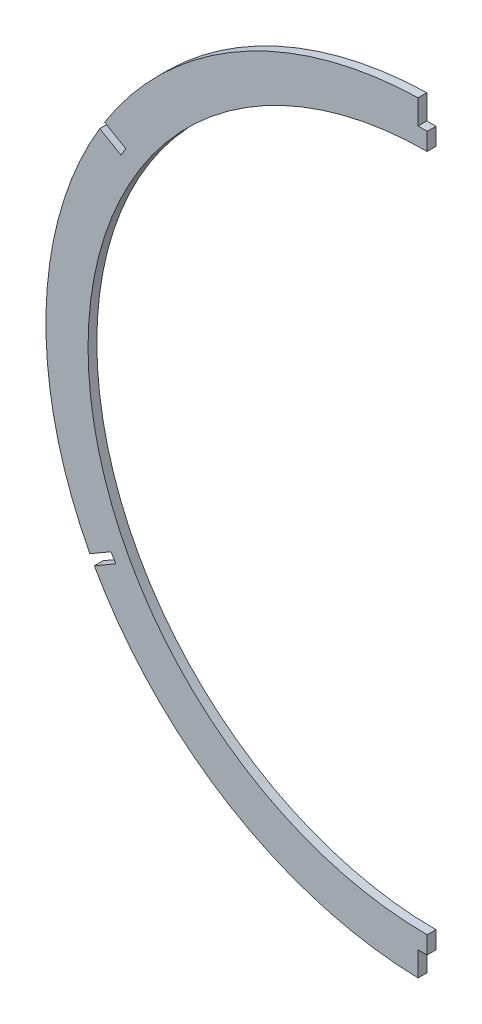
SolidWorks part; units mm, degrees
material "Plywood"
ref_plane "Front Plane" through (0, 0, 0) normal (0, 0, 1) x (1, 0, 0)
ref_plane "Top Plane" through (0, 0, 0) normal (0, 1, 0) x (1, 0, 0)
ref_plane "Right Plane" through (0, 0, 0) normal (1, 0, 0) x (0, 0, -1)
sketch "Sketch1" plane through (0, 0, 0) normal (0, 0, 1) x (1, 0, 0)
  line L0 (0, 0) -> (0, 499.9473) construction
  line L1 (0, -114.7984) -> (0, -129.4545) construction
  line L2 (0, -374.4718) -> (0, 404.2655) construction
  line L3 (-1.651, 142.9921) -> (-1.651, 150.6121) construction
  line L4 (1.651, 142.9921) -> (1.651, 150.6121) construction
  line L5 (-1.651, 142.9921) -> (1.651, 142.9921) construction
  line L6 (136.2041, -53.806) -> (0.0002, 24.7625) construction
  line L7 (-136.2076, -53.7991) -> (0.0002, 24.7625) construction
  line L8 (136.2041, -53.806) -> (0.0002, 24.7625) construction
  line L9 (-136.2076, -53.7991) -> (0.0002, 24.7625) construction
  line L10 (-125.0584, -45.4626) -> (-118.4576, -41.6554) construction
  line L11 (-123.6259, -48.4483) -> (-116.8078, -44.5157) construction
  line L12 (-118.4576, -41.6554) -> (-116.8078, -44.5157) construction
  line L13 (-124.1455, -48.7479) -> (-123.6847, -48.4822) construction
  line L14 (-123.6847, -48.4822) -> (-123.6259, -48.4483) construction
  line L15 (-125.7952, -45.8876) -> (-125.1113, -45.4931) construction
  line L16 (-125.1113, -45.4931) -> (-125.0584, -45.4626) construction
  line L17 (125.4797, -45.7137) -> (125.1075, -45.499) construction
  line L18 (123.8298, -48.5739) -> (123.6807, -48.488) construction
  line L19 (117.0223, -44.647) -> (118.6722, -41.7868) construction
  line L20 (123.6807, -48.488) -> (123.6228, -48.4545) construction
  line L21 (123.6228, -48.4545) -> (117.0223, -44.647) construction
  line L22 (125.1075, -45.499) -> (125.0554, -45.4689) construction
  line L23 (125.0554, -45.4689) -> (118.6722, -41.7868) construction
  line L24 (-107.079, -46.8884) -> (-120.3798, -54.5735)
  line L25 (-108.6638, -44.1348) -> (-121.9647, -51.8199)
  line L28 (-115.4206, -47.9666) -> (-121.9445, -51.7361) construction
  line L29 (-120.2754, -54.5131) -> (-108.646, -44.1245) construction
  line L30 (-114.4607, -49.3188) -> (-122.1124, -53.7399) construction
  line L31 (-113.7686, -50.8257) -> (-120.3665, -54.6379) construction
  line L32 (-115.4206, -47.9666) -> (-113.7686, -50.8257) construction
  line L33 (106.3137, -46.4532) -> (129.9098, -60.0883)
  line L34 (107.9004, -43.7007) -> (131.505, -57.3407)
  line L35 (129.9098, -60.0883) -> (131.505, -57.3407)
  line L36 (129.9098, -60.0883) -> (131.505, -57.3407) construction
  line L37 (107.9004, -43.7007) -> (131.505, -57.3407) construction
  line L38 (106.3137, -46.4532) -> (129.9098, -60.0883) construction
  line L39 (129.9098, -60.0883) -> (107.9004, -43.7007) construction
  line L40 (118.9051, -51.8945) -> (101.8722, -42.0519) construction
  line L41 (120.3631, -54.6438) -> (113.7655, -50.8313)
  line L42 (122.0152, -51.7848) -> (122.0057, -51.7794) construction
  line L43 (113.7655, -50.8313) -> (115.4176, -47.9723)
  line L44 (122.0057, -51.7794) -> (121.9413, -51.7421) construction
  line L45 (121.9413, -51.7421) -> (115.4176, -47.9723)
  line L46 (-108.6638, -44.1348) -> (-121.9647, -51.8199)
  line L47 (-107.079, -46.8884) -> (-120.3798, -54.5735)
  arc A0 (-1.651, 150.6121) -> (-125.0584, -45.4626) centre (0, 12.7) ccw
  circle A1 centre (0, 12.7) radius 120.904
  arc A2 (0, 150.622) -> (-1.651, 150.6121) centre (0, 12.7) ccw
  circle A3 centre (0, 12.7) radius 137.922 construction
  arc A4 (1.651, 150.6121) -> (0, 150.622) centre (0, 12.7) ccw
  arc A5 (-124.3508, -46.9604) -> (-123.6259, -48.4483) centre (0, 12.7) ccw
  arc A6 (-123.6259, -48.4483) -> (-121.9445, -51.7361) centre (0, 12.7) ccw
  arc A7 (-125.0584, -45.4626) -> (-124.3508, -46.9604) centre (0, 12.7) ccw
  arc A8 (124.3477, -46.9667) -> (125.0554, -45.4689) centre (0, 12.7) ccw
  arc A9 (125.0554, -45.4689) -> (1.651, 150.6121) centre (0, 12.7) ccw
  arc A10 (123.6228, -48.4545) -> (124.3477, -46.9667) centre (0, 12.7) ccw
  arc A11 (-121.9153, -51.7914) -> (-121.1641, -53.1919) centre (0, 12.7) ccw
  arc A12 (-120.3665, -54.6379) -> (120.3631, -54.6438) centre (0, 12.7) ccw
  arc A13 (-121.9445, -51.7361) -> (-121.9153, -51.7914) centre (0, 12.7) ccw
  arc A14 (-121.1641, -53.1919) -> (-120.3827, -54.6089) centre (0, 12.7) ccw
  arc A15 (-120.3827, -54.6089) -> (-120.397, -54.5834) centre (0, 12.7) ccw construction
  arc A16 (-120.397, -54.5834) -> (-120.3665, -54.6379) centre (0, 12.7) ccw construction
  arc A17 (120.3936, -54.5893) -> (121.0149, -53.4654) centre (0, 12.7) ccw construction
  arc A18 (121.9413, -51.7421) -> (123.6228, -48.4545) centre (0, 12.7) ccw
  arc A19 (120.3631, -54.6438) -> (120.3936, -54.5893) centre (0, 12.7) ccw construction
  arc A20 (121.0149, -53.4654) -> (121.9121, -51.7974) centre (0, 12.7) ccw construction
  arc A21 (121.9121, -51.7974) -> (121.9413, -51.7421) centre (0, 12.7) ccw construction
  spline S0 degree 3 poles (106.3137, -46.4532) (106.8426, -45.5357) (107.3715, -44.6182) (107.9004, -43.7007) knots 0 0 0 0 1 1 1 1 weights 1 1 1 1
  spline S1 degree 3 poles (-66.0123, 133.6164) (-70.0128, 131.4329) (-73.8716, 129.0699) (-81.3156, 123.9975) (-84.9009, 121.288) (-91.7995, 115.5249) (-95.113, 112.4712) (-99.0811, 108.4341) (-99.866, 107.6157) (-101.4182, 105.9565) (-102.1865, 105.1147) (-104.4569, 102.5643) (-105.9223, 100.8334) (-110.1768, 95.5512) (-115.4725, 88.2691) (-120.0285, 80.5179) (-123.1654, 74.5269) (-124.1643, 72.5002) (-125.5914, 69.415) (-126.0551, 68.3791) (-126.9587, 66.292) (-127.3989, 65.2397) (-129.5278, 59.9684) (-131.0098, 55.7) (-133.5456, 47.0638) (-134.5993, 42.696) (-136.2795, 33.8613) (-136.906, 29.3944) (-137.415, 23.7472) (-137.5031, 22.6146) (-137.6514, 20.3429) (-137.7116, 19.2049) (-137.8496, 15.7999) (-137.8852, 13.5361) (-137.8263, 6.7629) (-137.3062, -2.2197) (-135.9163, -11.1068) (-134.5433, -17.7359) (-134.0304, -19.9395) (-132.8922, -24.3345) (-132.2653, -26.5303) (-130.2347, -33.03) (-128.6774, -37.2656) (-126.1245, -43.2881) (-125.286, -45.1501) (-124.4066, -46.9926) knots 0 0 0 0 0.03125 0.03125 0.0625 0.0625 0.09375 0.09375 0.101563 0.101563 0.109375 0.109375 0.125 0.125 0.15625 0.1875 0.1875 0.203125 0.203125 0.210938 0.210938 0.21875 0.21875 0.25 0.25 0.28125 0.28125 0.3125 0.3125 0.320313 0.320313 0.328125 0.328125 0.34375 0.34375 0.375 0.40625 0.40625 0.421875 0.421875 0.4375 0.4375 0.46875 0.46875 0.48295 0.48295 0.48295 0.48295 construction
  spline S2 degree 3 poles (-2953.7904, 2461.9899) (-820.777, 189.8449) (-138.9507, -249.535) (81.4542, -98.9353) (85.033, -96.2237) (91.9188, -90.4573) (95.2258, -87.4025) (99.1858, -83.3647) (99.9691, -82.5461) (101.5182, -80.8868) (102.2849, -80.0449) (104.5506, -77.4941) (106.013, -75.7632) (110.2586, -70.4809) (112.9006, -66.8403) (117.8152, -59.3254) (120.0877, -55.4512) (123.2166, -49.4629) (124.2129, -47.4373) (125.6361, -44.3538) (126.0986, -43.3185) (126.9997, -41.2327) (127.4386, -40.181) (129.5618, -34.9121) (131.0396, -30.646) (133.5674, -22.0152) (134.6173, -17.6505) (136.2906, -8.8227) (136.914, -4.3596) (137.4197, 1.2823) (137.5071, 2.4139) (137.6542, 4.6834) (137.7138, 5.8206) (137.85, 9.2232) (137.8846, 11.4853) (137.8228, 18.2533) (137.2995, 27.2283) (135.9081, 36.1069) (134.5347, 42.7292) (134.0218, 44.9305) (132.8839, 49.3207) (132.2571, 51.5145) (130.2267, 58.0093) (128.67, 62.2416) (125.1615, 70.5162) (123.2097, 74.5586) (118.9108, 82.4534) (116.5637, 86.3058) (113.3753, 90.999) (112.7241, 91.9325) (111.3996, 93.7822) (110.7272, 94.697) (108.6802, 97.4113) (107.2757, 99.181) (102.9447, 104.3725) (96.8571, 110.9816) (90.1513, 116.9722) (84.8861, 121.2292) (83.0917, 122.6088) (80.3399, 124.6181) (79.4113, 125.2786) (77.543, 126.5731) (76.6028, 127.2075) (71.8708, 130.3161) (67.9881, 132.6004) (60.0328, 136.7739) (55.9603, 138.6631) (47.6249, 142.0446) (43.3619, 143.537) (37.9102, 145.1462) (36.8136, 145.4551) (34.6205, 146.0438) (33.5224, 146.3241) (30.2234, 147.1229) (28.0179, 147.5997) (21.3832, 148.8649) (16.9358, 149.4889) (7.993, 150.3014) (3.4975, 150.4899) (-3.2824, 150.4396) (-5.5486, 150.3672) (-10.0934, 150.1088) (-12.3559, 149.9236) (-19.101, 149.2046) (-23.5473, 148.5072) (-32.3412, 146.6856) (-36.6887, 145.5614) (-43.1354, 143.5526) (-45.2718, 142.8291) (-49.5193, 141.273) (-51.6323, 140.4395) (-369.2659, 5.9249) (-132.0865, -1278.1783) (677.8124, -3754.3927) knots -1.791229 -1.791229 -1.791229 -1.791229 0.03125 0.03125 0.0625 0.0625 0.09375 0.09375 0.101563 0.101563 0.109375 0.109375 0.125 0.125 0.15625 0.15625 0.1875 0.1875 0.203125 0.203125 0.210938 0.210938 0.21875 0.21875 0.25 0.25 0.28125 0.28125 0.3125 0.3125 0.320313 0.320313 0.328125 0.328125 0.34375 0.34375 0.375 0.40625 0.40625 0.421875 0.421875 0.4375 0.4375 0.46875 0.46875 0.5 0.5 0.53125 0.53125 0.539062 0.539062 0.546875 0.546875 0.5625 0.5625 0.59375 0.625 0.625 0.640625 0.640625 0.648437 0.648437 0.65625 0.65625 0.6875 0.6875 0.71875 0.71875 0.75 0.75 0.757812 0.757812 0.765625 0.765625 0.78125 0.78125 0.8125 0.8125 0.84375 0.84375 0.859375 0.859375 0.875 0.875 0.90625 0.90625 0.9375 0.9375 0.953125 0.953125 0.96875 0.96875 3.320852 3.320852 3.320852 3.320852 only from (66.1767, -108.566) to (-66.0123, 133.6164)
  spline S3 degree 3 poles (66.1767, -108.566) (70.1708, -106.3789) (74.0231, -104.0129) (81.4542, -98.9353) (85.033, -96.2237) (91.9188, -90.4573) (95.2258, -87.4025) (99.1858, -83.3647) (99.9691, -82.5461) (101.5182, -80.8868) (102.2849, -80.0449) (104.5506, -77.4941) (106.013, -75.7632) (110.2586, -70.4809) (112.9006, -66.8403) (117.8152, -59.3254) (120.0877, -55.4512) (123.2166, -49.4629) (124.2129, -47.4373) (125.6361, -44.3538) (126.0986, -43.3185) (126.9997, -41.2327) (127.4386, -40.181) (129.5618, -34.9121) (131.0396, -30.646) (133.5674, -22.0152) (134.6173, -17.6505) (136.2906, -8.8227) (136.914, -4.3596) (137.4197, 1.2823) (137.5071, 2.4139) (137.6542, 4.6834) (137.7138, 5.8206) (137.85, 9.2232) (137.8846, 11.4853) (137.8228, 18.2533) (137.2995, 27.2283) (135.9081, 36.1069) (134.5347, 42.7292) (134.0218, 44.9305) (132.8839, 49.3207) (132.2571, 51.5145) (130.2267, 58.0093) (128.67, 62.2416) (125.1615, 70.5162) (123.2097, 74.5586) (118.9108, 82.4534) (116.5637, 86.3058) (113.3753, 90.999) (112.7241, 91.9325) (111.3996, 93.7822) (110.7272, 94.697) (108.6802, 97.4113) (107.2757, 99.181) (102.9447, 104.3725) (96.8571, 110.9816) (90.1513, 116.9722) (84.8861, 121.2292) (83.0917, 122.6088) (80.3399, 124.6181) (79.4113, 125.2786) (77.543, 126.5731) (76.6028, 127.2075) (71.8708, 130.3161) (67.9881, 132.6004) (60.0328, 136.7739) (55.9603, 138.6631) (47.6249, 142.0446) (43.3619, 143.537) (37.9102, 145.1462) (36.8136, 145.4551) (34.6205, 146.0438) (33.5224, 146.3241) (30.2234, 147.1229) (28.0179, 147.5997) (21.3832, 148.8649) (16.9358, 149.4889) (7.993, 150.3014) (3.4975, 150.4899) (-3.2824, 150.4396) (-5.5486, 150.3672) (-10.0934, 150.1088) (-12.3559, 149.9236) (-19.101, 149.2046) (-23.5473, 148.5072) (-32.3412, 146.6856) (-36.6887, 145.5614) (-43.1354, 143.5526) (-45.2718, 142.8291) (-49.5193, 141.273) (-51.6323, 140.4395) (-57.9206, 137.7764) (-62.0153, 135.798) (-66.0123, 133.6164) knots 0 0 0 0 0.03125 0.03125 0.0625 0.0625 0.09375 0.09375 0.101563 0.101563 0.109375 0.109375 0.125 0.125 0.15625 0.15625 0.1875 0.1875 0.203125 0.203125 0.210938 0.210938 0.21875 0.21875 0.25 0.25 0.28125 0.28125 0.3125 0.3125 0.320313 0.320313 0.328125 0.328125 0.34375 0.34375 0.375 0.40625 0.40625 0.421875 0.421875 0.4375 0.4375 0.46875 0.46875 0.5 0.5 0.53125 0.53125 0.539062 0.539062 0.546875 0.546875 0.5625 0.5625 0.59375 0.625 0.625 0.640625 0.640625 0.648437 0.648437 0.65625 0.65625 0.6875 0.6875 0.71875 0.71875 0.75 0.75 0.757812 0.757812 0.765625 0.765625 0.78125 0.78125 0.8125 0.8125 0.84375 0.84375 0.859375 0.859375 0.875 0.875 0.90625 0.90625 0.9375 0.9375 0.953125 0.953125 0.96875 0.96875 1 1 1 1 construction
  spline S4 degree 3 poles (-124.4066, -46.9926) (-124.169, -47.4906) (-123.9283, -47.9871) (-123.6847, -48.4822) knots 0.48295 0.48295 0.48295 0.48295 0.486788 0.486788 0.486788 0.486788 construction
  spline S5 degree 3 poles (-123.6847, -48.4822) (-122.846, -50.1865) (-121.9718, -51.874) (-118.9108, -57.4955) (-116.5612, -61.3517) (-113.369, -66.0497) (-112.7169, -66.9844) (-111.3913, -68.8351) (-110.7184, -69.7503) (-108.6697, -72.4662) (-107.264, -74.2369) (-102.929, -79.4315) (-96.8353, -86.0447) (-90.1214, -92.0392) (-84.8493, -96.299) (-83.0524, -97.6795) (-80.2967, -99.6899) (-79.367, -100.3507) (-77.4971, -101.6451) (-76.5559, -102.2795) (-71.8198, -105.3881) (-67.9332, -107.6723) (-59.9695, -111.8452) (-55.8924, -113.7339) (-47.5468, -117.114) (-43.2782, -118.6053) (-37.8188, -120.2127) (-36.7216, -120.521) (-34.5268, -121.1085) (-33.4279, -121.3881) (-30.1264, -122.185) (-27.9191, -122.6605) (-21.2788, -123.9216) (-16.8274, -124.5426) (-7.8757, -125.3484) (-3.3755, -125.5332) (3.4122, -125.4766) (5.6812, -125.4019) (10.231, -125.1387) (12.493, -124.9512) (19.2413, -124.2249) (23.6899, -123.5224) (32.4889, -121.6898) (36.8393, -120.5597) (43.2904, -118.5412) (45.4283, -117.8143) (48.6163, -116.6419) (49.6759, -116.2374) (51.7885, -115.4006) (52.8426, -114.968) (58.0839, -112.7404) (62.1792, -110.755) (66.1767, -108.566) knots 0.486788 0.486788 0.486788 0.486788 0.5 0.5 0.53125 0.53125 0.539062 0.539062 0.546875 0.546875 0.5625 0.5625 0.59375 0.625 0.625 0.640625 0.640625 0.648437 0.648437 0.65625 0.65625 0.6875 0.6875 0.71875 0.71875 0.75 0.75 0.757812 0.757812 0.765625 0.765625 0.78125 0.78125 0.8125 0.8125 0.84375 0.84375 0.859375 0.859375 0.875 0.875 0.90625 0.90625 0.9375 0.9375 0.953125 0.953125 0.960937 0.960937 0.96875 0.96875 1 1 1 1 construction
  spline S6 degree 3 poles (-108.6638, -44.1348) (-108.1355, -45.0527) (-107.6073, -45.9705) (-107.079, -46.8884) knots 0 0 0 0 1 1 1 1 weights 1 1 1 1
  spline S7 degree 3 poles (-121.9647, -51.8199) (-121.4364, -52.7377) (-120.9081, -53.6556) (-120.3798, -54.5735) knots 0 0 0 0 1 1 1 1 weights 1 1 1 1
  spline S8 degree 3 poles (-1893.2868, -3504.9508) (-555.1038, -1197.2913) (777.7443, 1114.8675) (2098.5226, 3419.8495) knots -1257.715582 -1257.715582 -1257.715582 -1257.715582 1261.2826 1261.2826 1261.2826 1261.2826 weights 1.001261 0.999578 0.99958 1.001266 only from (106.3137, -46.4532) to (107.9004, -43.7007)
  spline S9 degree 3 poles (-121.8597, -51.7592) (-121.5948, -52.2177) (-121.3299, -52.6762) (-121.065, -53.1347) knots 0 0 0 0 0.5 0.5 0.5 0.5 weights 1 1 1 1 construction
  spline S12 degree 3 poles (-2107.5184, 3411.1282) (-794.411, 1112.1626) (537.2029, -1201.4874) (1876.5356, -3511.0638) knots -1261.624621 -1261.624621 -1261.624621 -1261.624621 1257.384167 1257.384167 1257.384167 1257.384167 weights 1.00204 0.999326 0.99932 1.002023 only from (-121.9647, -51.8199) to (-120.3798, -54.5735)
  spline S13 degree 3 poles (-2094.7969, 3419.3607) (-780.7303, 1119.4679) (550.7427, -1194.0569) (1889.8709, -3504.2883) knots -1261.518414 -1261.518414 -1261.518414 -1261.518414 1257.484402 1257.484402 1257.484402 1257.484402 weights 1.00184 0.999392 0.999387 1.001825 only from (-108.6638, -44.1348) to (-107.079, -46.8884)
  point P7 (0, -125.5003)
  point P8 (0, 150.4602)
  point P25 (-125.0584, -45.4626)
  point P38 (123.6228, -48.4545)
  dimension "D2" = 275.844
  dimension "D1" = 275.9605
  dimension "D3" = 12.7
  dimension "D5" = 3.302
  dimension "D6" = 7.62
  dimension "D7" = 3.302
  dimension "D8" = 7.62
  dimension "D9" = 3.302
  dimension "D10" = 7.62
  dimension "D11" = 3.302
  dimension "D12" = 7.62
  dimension "D13" = 3.302
  dimension "D14" = 7.62
  dimension "D4" = 17.018
sketch "Sketch2" plane through (248.2736, -245.0135, 0) normal (0, 0, -1) x (0, -1, 0)
  line L3 (-245.0135, 248.2736) -> (-427.6569, 248.2736) construction
  circle A1 centre (-257.7135, 248.2736) radius 137.922
  circle A16 centre (-257.7135, 248.2736) radius 122.682
  dimension "D1" = 12.7
  dimension "D2" = 275.844
  dimension "D3" = 15.24
extrude "Boss-Extrude2" add sketch "Sketch2" along normal mid plane 3.175
sketch "Sketch3" plane through (0, 0, 0) normal (1, 0, 0) x (0, 0, -1)
  line L1 (-141.282, 263.3615) -> (149.6958, 263.3615)
  line L2 (-141.282, 263.3615) -> (-141.282, -241.4673)
  line L3 (-141.282, -241.4673) -> (149.6958, -241.4673)
  line L4 (149.6958, 263.3615) -> (149.6958, -241.4673)
extrude "Cut-Extrude1" cut sketch "Sketch3" along normal through all
sketch "Sketch5" plane through (0, 0, 1.5875) normal (0, 0, 1) x (1, 0, 0)
  line L0 (0, 0) -> (0, 135.382) construction
  line L1 (0, 135.382) -> (0, 141.732) construction
  line L2 (-3.302, 141.732) -> (3.302, 141.732)
  line L3 (0, 141.732) -> (0, 151.892)
  line L4 (-3.302, 151.892) -> (3.302, 151.892)
  line L5 (3.302, 141.732) -> (3.302, 151.892)
  line L6 (103.544, 78.6136) -> (105.2331, 75.688) construction
  line L7 (104.3885, 77.1508) -> (0, 16.882) construction
  line L8 (103.544, 78.6136) -> (105.2331, 75.688) construction
  line L9 (103.544, 78.6136) -> (109.0433, 81.7886) construction
  line L10 (105.2331, 75.688) -> (110.7324, 78.863) construction
  line L11 (109.0433, 81.7886) -> (110.7324, 78.863) construction
  line L12 (109.0433, 81.7886) -> (110.7324, 78.863)
  line L13 (109.0433, 81.7886) -> (118.3449, 87.1589)
  line L14 (110.7324, 78.863) -> (120.034, 84.2333)
  line L15 (118.3449, 87.1589) -> (120.034, 84.2333)
  line L16 (0, 16.882) -> (0, -109.982) construction
  line L17 (0, -109.982) -> (0, -116.332) construction
  line L18 (-3.302, -116.332) -> (3.302, -116.332)
  line L19 (0, -116.332) -> (0, -126.6527)
  line L20 (-3.302, -126.6527) -> (3.302, -126.6527)
  line L21 (3.302, -116.332) -> (3.302, -126.6527)
  line L22 (107.1657, -46.9405) -> (108.8548, -44.0149) construction
  line L23 (108.0103, -45.4777) -> (0, 16.882) construction
  line L24 (107.1657, -46.9405) -> (108.8548, -44.0149) construction
  line L25 (107.1657, -46.9405) -> (112.665, -50.1155) construction
  line L26 (108.8548, -44.0149) -> (114.3541, -47.1899) construction
  line L27 (112.665, -50.1155) -> (114.3541, -47.1899) construction
  line L28 (112.665, -50.1155) -> (114.3541, -47.1899)
  line L29 (112.665, -50.1155) -> (134.6621, -62.8155)
  line L30 (114.3541, -47.1899) -> (136.3512, -59.8899)
  line L31 (134.6621, -62.8155) -> (136.3512, -59.8899)
  line L32 (-112.665, -50.1155) -> (-114.3541, -47.1899) construction
  line L33 (-108.8548, -44.0149) -> (-114.3541, -47.1899) construction
  line L34 (-107.1657, -46.9405) -> (-112.665, -50.1155) construction
  line L35 (-107.1657, -46.9405) -> (-108.8548, -44.0149) construction
  line L36 (-108.0103, -45.4777) -> (0, 16.882) construction
  line L37 (-107.1657, -46.9405) -> (-108.8548, -44.0149) construction
  line L38 (-109.0433, 81.7886) -> (-110.7324, 78.863) construction
  line L39 (-105.2331, 75.688) -> (-110.7324, 78.863) construction
  line L40 (-103.544, 78.6136) -> (-109.0433, 81.7886) construction
  line L41 (-103.544, 78.6136) -> (-105.2331, 75.688) construction
  line L42 (-104.3885, 77.1508) -> (0, 16.882) construction
  line L43 (-103.544, 78.6136) -> (-105.2331, 75.688) construction
  line L44 (-134.6621, -62.8155) -> (-136.3512, -59.8899)
  line L45 (-114.3541, -47.1899) -> (-136.3512, -59.8899)
  line L46 (-112.665, -50.1155) -> (-134.6621, -62.8155)
  line L47 (-112.665, -50.1155) -> (-114.3541, -47.1899)
  line L48 (-3.302, -116.332) -> (-3.302, -126.6527)
  line L49 (-118.3449, 87.1589) -> (-120.034, 84.2333)
  line L50 (-110.7324, 78.863) -> (-120.034, 84.2333)
  line L51 (-109.0433, 81.7886) -> (-118.3449, 87.1589)
  line L52 (-109.0433, 81.7886) -> (-110.7324, 78.863)
  line L53 (-3.302, 141.732) -> (-3.302, 151.892)
  point P9 (104.3885, 77.1508)
  point P19 (108.0103, -45.4777)
  line M25 (0, 135.382) -> (0, 150.622)
  arc M26 (0, 150.622) -> (0, -125.222) centre (0, 12.7) ccw
  line M27 (0, -125.222) -> (0, -109.982)
  dimension "D1" = 16.882
  dimension "D2" = 60
  dimension "D3" = 60
  dimension "D4" = 135.382
  dimension "D5" = 120.5375
  dimension "D6" = 124.7195
  dimension "D7" = 126.864
  dimension "D8" = 6.35
  dimension "D9" = 6.35
  dimension "D10" = 10.7406
  dimension "D11" = 3.3782
  dimension "D12" = 6.35
  dimension "D13" = 3.3782
  dimension "D14" = 6.35
  dimension "D15" = 3.302
  dimension "D16" = 10.3207
  dimension "D17" = 3.302
extrude "Cut-Extrude2" cut sketch "Sketch5" against normal through all contours L53 L2 M25 M26 | L52 L51 L50 M26 | L46 L47 L45 M26 | L18 L48 M26 M27
equation "\"slotwidth\"=0.13"
equation "\"D11@Sketch1\"=\"slotwidth\""
